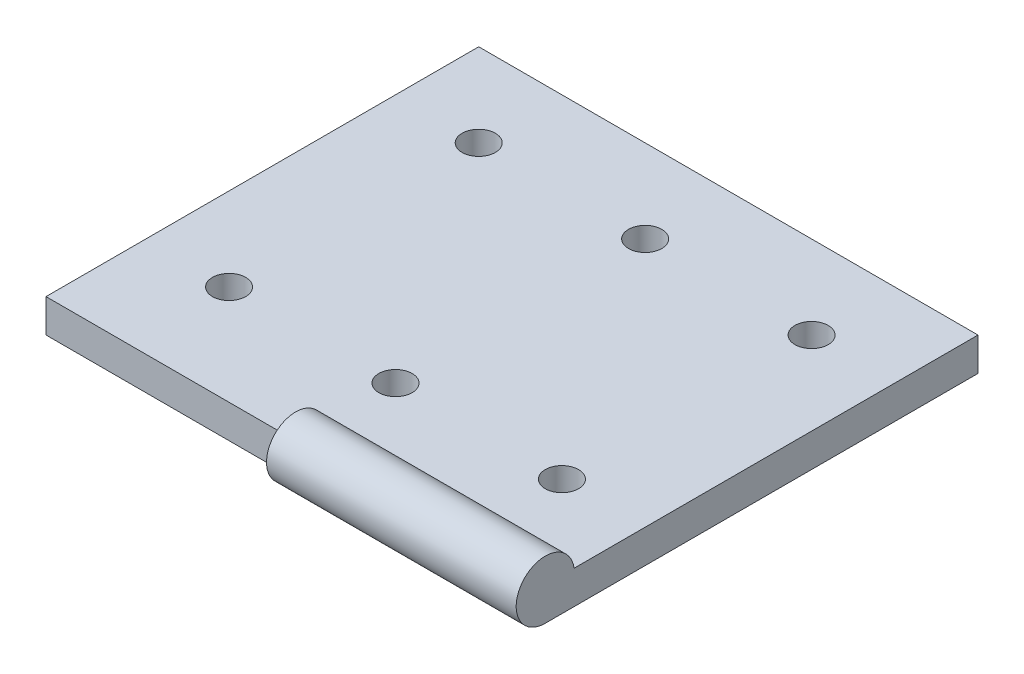
SolidWorks part; units mm, degrees
ref_plane "Front Plane" through (0, 0, 0) normal (0, 0, 1) x (1, 0, 0)
ref_plane "Top Plane" through (0, 0, 0) normal (0, 1, 0) x (1, 0, 0)
ref_plane "Right Plane" through (0, 0, 0) normal (1, 0, 0) x (0, 0, -1)
sketch "Sketch1" plane through (0, 0, 0) normal (0, 1, 0) x (1, 0, 0)
  line L2 (18.0696, -160.0434) -> (3.0696, -160.0434)
  line L3 (18.0696, -160.0434) -> (18.0696, -173.0434)
  line L4 (18.0696, -173.0434) -> (3.0696, -173.0434)
  line L5 (3.0696, -160.0434) -> (3.0696, -173.0434)
  dimension "D1" = 13
  dimension "D2" = 15
extrude "Boss-Extrude1" add sketch "Sketch1" along normal blind 1
sketch "Sketch2" plane through (18.0696, 0, 0) normal (1, 0, 0) x (0, 0, -1)
  circle A0 centre (-173.0434, 0.875) radius 0.875
  point P4 (0, 0)
  dimension "D1" = 1.75
extrude "Boss-Extrude2" add sketch "Sketch2" against normal blind 7.5
sketch "Sketch3" plane through (0, 1, 0) normal (0, 1, 0) x (1, 0, 0)
  line L0 (18.0696, -160.0434) -> (3.0696, -160.0434) construction
  line L1 (18.0696, -172.1774) -> (18.0696, -160.0434) construction
  line L2 (15.5696, -162.5434) -> (15.5696, -170.0434) construction
  line L3 (15.5696, -170.0434) -> (5.5696, -170.0434) construction
  line L4 (5.5696, -170.0434) -> (5.5696, -162.5434) construction
  line L5 (5.5696, -162.5434) -> (15.5696, -162.5434) construction
  line L6 (3.0696, -160.0434) -> (3.0696, -173.0434) construction
  line L7 (3.0696, -173.0434) -> (10.5696, -173.0434) construction
  circle A0 centre (15.5696, -162.5434) radius 0.5
  circle A1 centre (15.5696, -170.0434) radius 0.5
  circle A2 centre (10.5696, -162.5434) radius 0.5
  circle A3 centre (10.5696, -170.0434) radius 0.5
  circle A4 centre (5.5696, -162.5434) radius 0.5
  circle A5 centre (5.5696, -170.0434) radius 0.5
  point P16 (0, 0)
  point P17 (10.5696, -162.5434)
  point P22 (0, 0)
  point P23 (10.5696, -170.0434)
  point P24 (10.5696, -170.0434)
  dimension "D1" = 1
  dimension "D2" = 2.5
  dimension "D3" = 2.5
  dimension "D4" = 2.5
  dimension "D5" = 10
extrude "Cut-Extrude1" cut sketch "Sketch3" against normal through all
